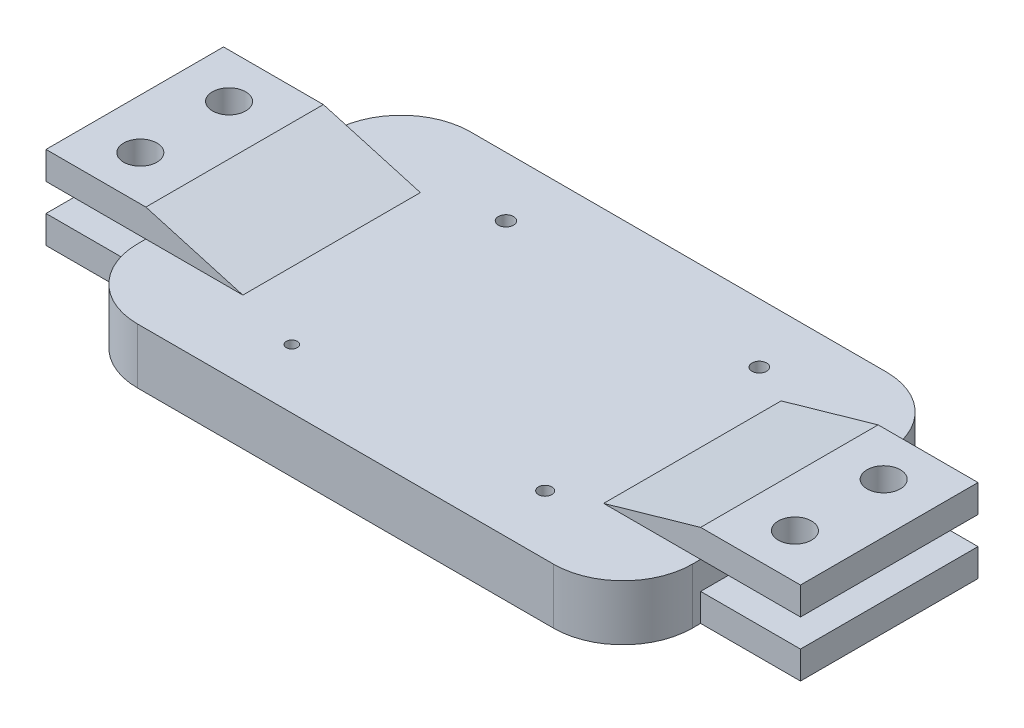
SolidWorks part; units mm, degrees
material "ABS"
ref_plane "Front Plane" through (0, 0, 0) normal (0, 0, 1) x (1, 0, 0)
ref_plane "Top Plane" through (0, 0, 0) normal (0, 1, 0) x (1, 0, 0)
ref_plane "Right Plane" through (0, 0, 0) normal (1, 0, 0) x (0, 0, -1)
sketch "Sketch1" plane through (0, 0, 0) normal (0, 1, 0) x (1, 0, 0)
  line L1 (-63.5, -38.1) -> (63.5, -38.1)
  line L2 (-63.5, -38.1) -> (-63.5, 38.1)
  line L3 (-63.5, 38.1) -> (63.5, 38.1)
  line L4 (63.5, -38.1) -> (63.5, 38.1)
  line L5 (-63.5, -38.1) -> (63.5, 38.1) construction
  line L6 (-63.5, 38.1) -> (63.5, -38.1) construction
  point P0 (0, 0)
  dimension "D1" = 127
  dimension "D2" = 76.2
extrude "Boss-Extrude1" add sketch "Sketch1" along normal blind 12.7
sketch "Sketch12" plane through (0, 12.7, 0) normal (0, 1, 0) x (1, 0, 0)
  line L1 (63.5, -38.1) -> (63.5, 38.1) construction
  line L2 (63.5, 38.1) -> (-63.5, 38.1) construction
  line L3 (47.625, 38.1) -> (63.5, 38.1)
  line L4 (63.5, 38.1) -> (63.5, 22.225)
  line L6 (-6.985, 0) -> (6.985, 0) construction
  line L7 (47.625, -38.1) -> (63.5, -38.1)
  line L8 (63.5, -38.1) -> (63.5, -22.225)
  line L9 (0, -6.985) -> (0, 6.985) construction
  line L10 (-63.5, -38.1) -> (-63.5, -22.225)
  line L11 (-47.625, -38.1) -> (-63.5, -38.1)
  line L12 (-63.5, 38.1) -> (-63.5, 22.225)
  line L13 (-47.625, 38.1) -> (-63.5, 38.1)
  circle A0 centre (47.625, 22.225) radius 15.875
  circle A1 centre (47.625, -22.225) radius 15.875
  circle A2 centre (-47.625, -22.225) radius 15.875
  circle A3 centre (-47.625, 22.225) radius 15.875
  line M5 (63.5, 38.1) -> (-63.5, 38.1)
  line M10 (-63.5, 38.1) -> (-63.5, -38.1)
  line M11 (-63.5, -38.1) -> (63.5, -38.1)
  line M12 (63.5, -38.1) -> (63.5, 38.1)
  dimension "D1" = 31.75
sketch "Sketch20" plane through (63.5, 0, 0) normal (1, 0, 0) x (0, 0, -1)
  line L0 (-38.1, 0) -> (38.1, 0) construction
  line L1 (20.32, 0) -> (-20.32, 0)
  line L2 (20.32, 0) -> (20.32, 6.35)
  line L3 (20.32, 6.35) -> (-20.32, 6.35)
  line L4 (-20.32, 0) -> (-20.32, 6.35)
  line L5 (38.1, 12.7) -> (6.35, 12.7) construction
  line L6 (20.32, 12.7) -> (-20.32, 12.7)
  line L7 (20.32, 12.7) -> (20.32, 19.05)
  line L8 (20.32, 19.05) -> (-20.32, 19.05)
  line L9 (-20.32, 12.7) -> (-20.32, 19.05)
  point P13 (0, 12.7)
  dimension "D1" = 6.35
  dimension "D2" = 20.32
  dimension "D3" = 20.32
  dimension "D4" = 6.35
  dimension "D5" = 20.32
  dimension "D6" = 40.64
extrude "Boss-Extrude7" add sketch "Sketch20" along normal blind 22.86 separate body
sketch "Sketch21" plane through (0, 19.05, 0) normal (0, 1, 0) x (1, 0, 0)
  line L0 (86.36, 20.32) -> (86.36, -20.32) construction
  line L1 (-6.985, 0) -> (6.985, 0) construction
  circle A0 centre (74.93, 10.16) radius 3.81
  circle A1 centre (74.93, -10.16) radius 3.81
  dimension "D1" = 7.62
  dimension "D5" = 7.62
  dimension "D2" = 11.43
  dimension "D3" = 10.16
  dimension "D4" = 20.32
  dimension "D6" = 11.43
extrude "Cut-Extrude17" cut sketch "Sketch21" against normal up to surface (19.05 mm away) up to face at (74.93, 0, 0)
sketch "Sketch19" plane through (0, 0, 0) normal (0, -1, 0) x (-1, 0, 0)
  circle A5 centre (-32.0993, 24.511) radius 1.6712
  circle A6 centre (25.9007, 24.511) radius 1.7336
  circle A7 centre (25.9007, -24.511) radius 1.269
  circle A8 centre (-32.0993, -24.511) radius 1.5453
  circle A9 centre (-32.0993, -24.511) radius 1.5453 construction
  circle A10 centre (-32.0993, 24.511) radius 1.6712 construction
  circle A11 centre (25.9007, 24.511) radius 1.7336 construction
  circle A12 centre (25.9007, -24.511) radius 1.269 construction
sketch "Sketch24" plane through (0, 0, 0) normal (0, 0, 1) x (1, 0, 0)
  line L0 (63.5, 19.05) -> (41.2964, 12.7)
  line L2 (41.2964, 12.7) -> (63.5, 12.7)
  line L3 (63.5, 12.7) -> (63.5, 19.05)
  line L4 (63.5, 12.7) -> (31.75, 12.7) construction
  point P3 (47.4685, 12.7)
  point P8 (43.3864, 12.7)
  dimension "D1" = 15.96
extrude "Boss-Extrude8" add sketch "Sketch24" along normal up to surface (20.32 mm away) and the other way up to surface (20.32 mm away) up to face at (74.93, 15.875, 20.32) other way up to face at (74.93, 15.875, -20.32)
extrude "Cut-Extrude18" cut sketch "Sketch19" against normal blind 42.672
extrude "Cut-Extrude19" cut sketch "Sketch12" against normal blind 42.672 contours A2 M10 M11 | A3 M10 M5 | A0 M12 M5 | A1 M12 M11
mirror "Mirror1" about plane through (0, 0, 0) normal (1, 0, 0) of "Cut-Extrude17", "Boss-Extrude8", "Boss-Extrude7"
